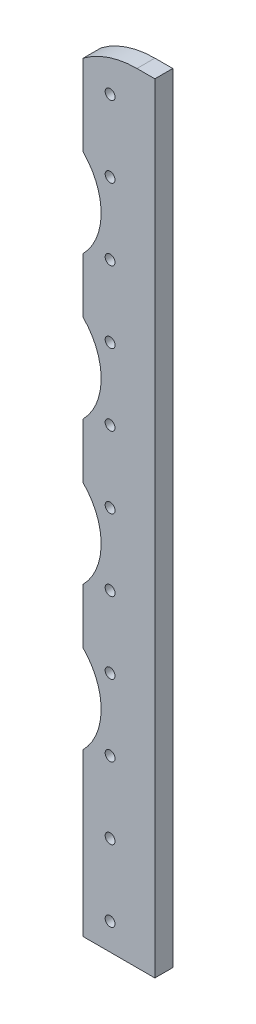
SolidWorks part; units mm, degrees
ref_plane "Front Plane" through (0, 0, 0) normal (0, 0, 1) x (1, 0, 0)
ref_plane "Top Plane" through (0, 0, 0) normal (0, 1, 0) x (1, 0, 0)
ref_plane "Right Plane" through (0, 0, 0) normal (1, 0, 0) x (0, 0, -1)
sketch "Sketch1" plane through (0, 0, 0) normal (0, 0, 1) x (1, 0, 0)
  line L1 (0, 0) -> (-25.4, 0)
  line L2 (0, 0) -> (0, 276.225)
  line L3 (0, 276.225) -> (-25.4, 276.225)
  line L4 (-25.4, 0) -> (-25.4, 276.225)
  dimension "D1" = 25.4
  dimension "D2" = 276.225
extrude "Boss-Extrude1" add sketch "Sketch1" along normal blind 6.35
sketch "Sketch2" plane through (0, 0, 6.35) normal (0, 0, 1) x (1, 0, 0)
  line L0 (0, 276.225) -> (-25.4, 276.225) construction
  line L1 (-6.35, 276.225) -> (-31.7633, 276.225)
  line L2 (-31.7633, 276.225) -> (-31.7633, 263.5073)
  arc A0 (-6.35, 276.225) -> (-31.7633, 263.5073) centre (-6.35, 244.475) ccw
  dimension "D1" = 31.75
  dimension "D2" = 6.35
extrude "Cut-Extrude1" cut sketch "Sketch2" against normal through all contours L1 L2 A0
sketch "Sketch3" plane through (0, 0, 6.35) normal (0, 0, 1) x (1, 0, 0)
  line L0 (0, 276.225) -> (-6.35, 276.225) construction
  line L1 (0, 0) -> (0, 276.225) construction
  circle A0 centre (-15.875, 263.525) radius 1.75
  dimension "D1" = 3.5
  dimension "D2" = 12.7
  dimension "D3" = 15.875
extrude "Cut-Extrude2" cut sketch "Sketch3" against normal through all
pattern_linear "LPattern1" count 11 spacing 25.4 along (0, -1, 0) of "Cut-Extrude2"
sketch "Sketch4" plane through (0, 0, 6.35) normal (0, 0, 1) x (1, 0, 0)
  line L0 (-15.875, 238.125) -> (-15.875, 212.725) construction
  line L1 (-15.875, 225.425) -> (-41.275, 225.425) construction
  circle A0 centre (-41.275, 225.425) radius 22.225
  dimension "D2" = 44.45
  dimension "D1" = 25.4
extrude "Cut-Extrude3" cut sketch "Sketch4" against normal through all
pattern_linear "LPattern2" count 4 spacing 50.8 along (0, -1, 0) of "Cut-Extrude3"
